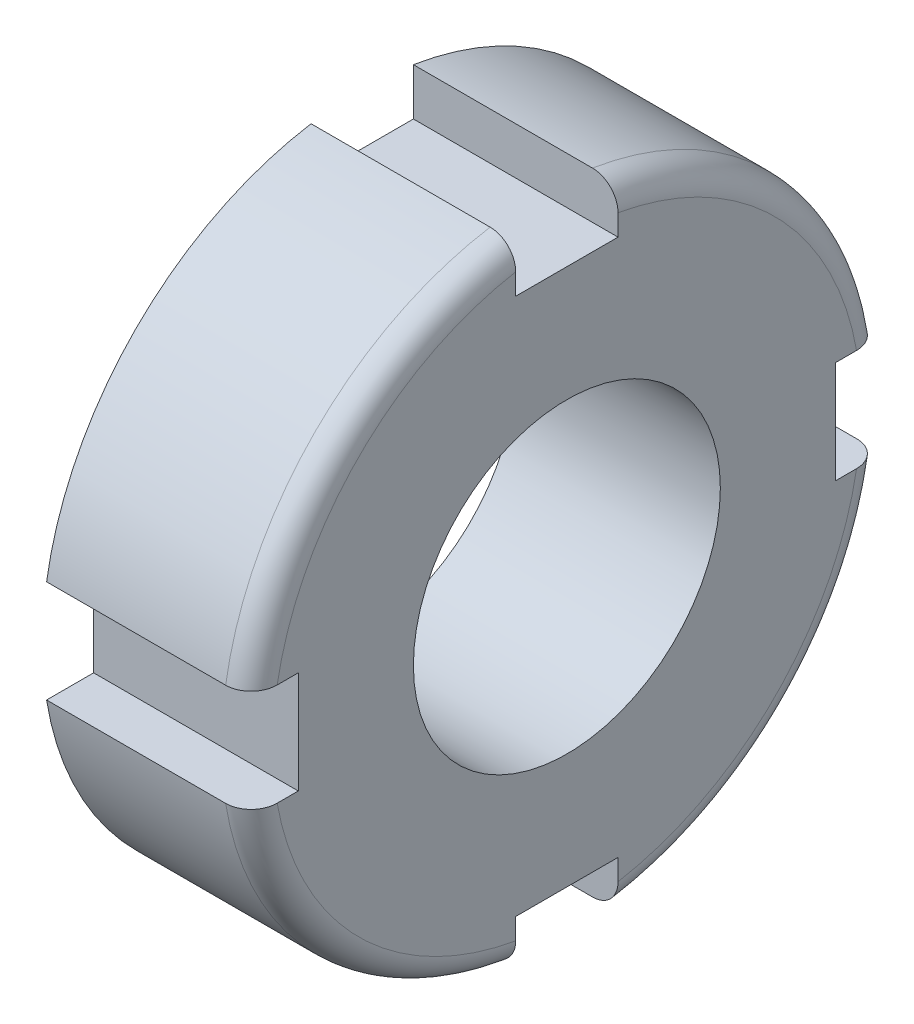
SolidWorks part; units mm, degrees
ref_plane "Front Plane" through (0, 0, 0) normal (0, 0, 1) x (1, 0, 0)
ref_plane "Top Plane" through (0, 0, 0) normal (0, 1, 0) x (1, 0, 0)
ref_plane "Right Plane" through (0, 0, 0) normal (1, 0, 0) x (0, 0, -1)
sketch "Sketch1" plane through (0, 0, 0) normal (1, 0, 0) x (0, 0, -1)
  circle A0 centre (0, 0) radius 12.5
  dimension "D1" = 25
extrude "Boss-Extrude1" add sketch "Sketch1" along normal blind 8
sketch "Sketch2" plane through (8, 0, 0) normal (1, 0, 0) x (0, 0, -1)
  circle A0 centre (0, 0) radius 6
  dimension "D1" = 12
extrude "Cut-Extrude1" cut sketch "Sketch2" against normal through all
fillet "Fillet1" radius 1 1 edges at (8, 0, -12.5)
sketch "Sketch3" plane through (8, 0, 0) normal (1, 0, 0) x (0, 0, -1)
  line L0 (0, 0) -> (0, 15.0362) construction
  line L2 (-2, 14.5) -> (2, 14.5)
  line L3 (-2, 14.5) -> (-2, 10.5)
  line L4 (-2, 10.5) -> (2, 10.5)
  line L5 (2, 14.5) -> (2, 10.5)
  line L6 (-2, 14.5) -> (2, 10.5) construction
  line L7 (-2, 10.5) -> (2, 14.5) construction
  circle A0 centre (0, 0) radius 12.5 construction
  point P3 (0, 12.5)
  dimension "D1" = 4
  dimension "D2" = 4
extrude "Cut-Extrude2" cut sketch "Sketch3" against normal through all
pattern_circular "CirPattern1" count 4 over 360 about axis through (0, 0, 0) along (1, 0, 0) of "Cut-Extrude2"
